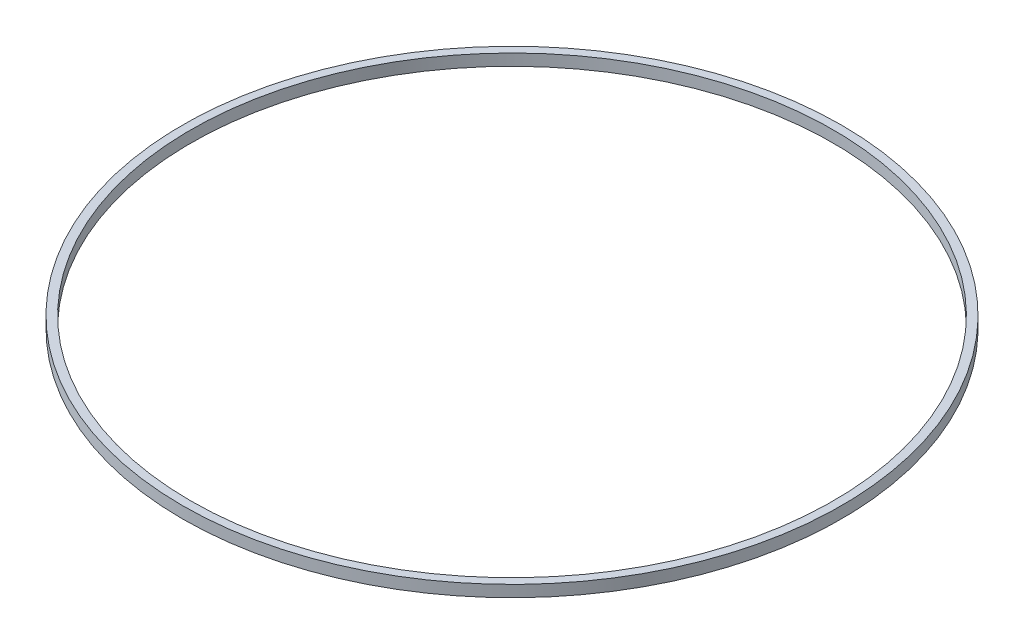
SolidWorks part; units mm, degrees
ref_plane "Front Plane" through (0, 0, 0) normal (0, 0, 1) x (1, 0, 0)
ref_plane "Top Plane" through (0, 0, 0) normal (0, 1, 0) x (1, 0, 0)
ref_plane "Right Plane" through (0, 0, 0) normal (1, 0, 0) x (0, 0, -1)
sketch "Sketch1" plane through (0, 0, 0) normal (0, 1, 0) x (1, 0, 0)
  circle A0 centre (0, 0) radius 100
  circle A1 centre (0, 0) radius 97.5
  dimension "D1" = 200
  dimension "D2" = 195
extrude "Boss-Extrude1" add sketch "Sketch1" along normal blind 3.5
sketch "Sketch2" plane through (0, 0, 0) normal (0, 0, 1) x (1, 0, 0)
  line L1 (-5.291, 35) -> (22.709, 35)
  line L2 (-5.291, 35) -> (-5.291, 5)
  line L3 (-5.291, 5) -> (22.709, 5)
  line L4 (22.709, 35) -> (22.709, 5)
  dimension "D1" = 5
  dimension "D2" = 30
  dimension "D3" = 28
